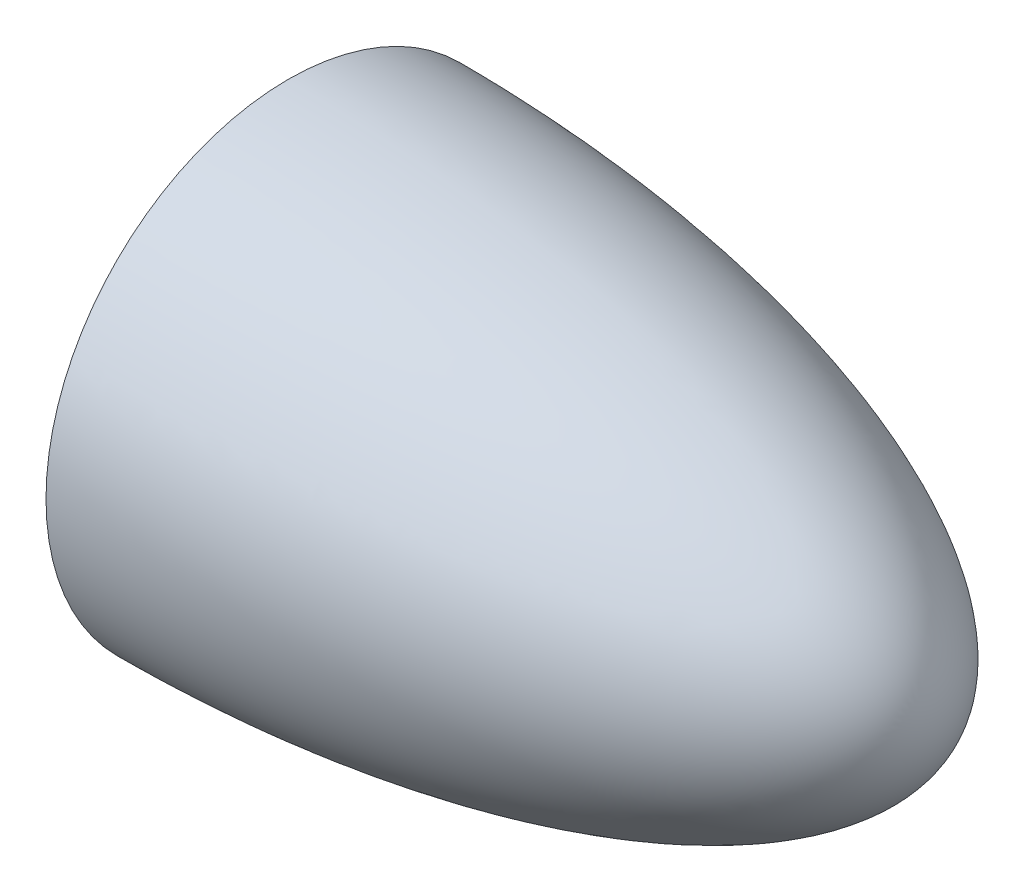
SolidWorks part; units mm, degrees
material "Custom Plastic"
ref_plane "Front Plane" through (0, 0, 0) normal (0, 0, 1) x (1, 0, 0)
ref_plane "Top Plane" through (0, 0, 0) normal (0, 1, 0) x (1, 0, 0)
ref_plane "Right Plane" through (0, 0, 0) normal (1, 0, 0) x (0, 0, -1)
sketch "Sketch1" plane through (0, 0, 0) normal (0, 0, 1) x (1, 0, 0)
  line L4 (0, 38.1) -> (0, 31.75)
  line L5 (95.25, 0) -> (101.6, 0)
  spline S0 degree 4 poles (-10.1599, 37.909) (-9.8428, 37.921) (-9.2082, 37.9439) (-7.937, 37.9857) (-6.3533, 38.028) (-4.7601, 38.0603) (-3.1781, 38.0826) (-1.9201, 38.0945) (-0.3504, 38.1013) (0.9584, 38.0999) (3.0623, 38.087) (4.8396, 38.0587) (7.3853, 38.0054) (10.2567, 37.9131) (13.2403, 37.7849) (16.1477, 37.6205) (18.6059, 37.4591) (20.5529, 37.3152) (22.9983, 37.1167) (25.9229, 36.8484) (29.3352, 36.4907) (33.225, 36.0189) (37.1079, 35.4822) (40.9801, 34.8783) (44.8413, 34.2043) (48.6886, 33.4569) (53.4783, 32.4264) (59.1889, 31.0263) (64.8414, 29.4022) (70.4117, 27.5165) (75.6688, 25.4757) (79.9302, 23.589) (84.0819, 21.4677) (88.0736, 19.0607) (91.0619, 16.9696) (93.6297, 14.8636) (95.7115, 12.8459) (97.2987, 11.0336) (98.5662, 9.3062) (99.542, 7.6977) (100.3319, 6.089) (100.9382, 4.4726) (101.3808, 2.7572) (101.5592, 1.389) (101.6, 0.4832) (101.6, 0) knots 0 0 0 0 0 0.010112 0.020223 0.040447 0.050558 0.06067 0.070782 0.080893 0.096491 0.11209 0.127688 0.143286 0.174482 0.205679 0.221277 0.236875 0.252473 0.268071 0.299268 0.330464 0.36166 0.392857 0.424053 0.45525 0.486446 0.517642 0.580035 0.642428 0.673624 0.70482 0.759552 0.790748 0.821944 0.853141 0.875573 0.896371 0.914156 0.929752 0.94371 0.956194 0.971147 0.984621 1 1 1 1 1 construction
  spline S1 degree 4 poles (0, 38.1) (0.4503, 38.1) (1.3323, 38.0976) (3.0623, 38.087) (4.8396, 38.0587) (7.3853, 38.0054) (10.2567, 37.9131) (13.2403, 37.7849) (16.1477, 37.6205) (18.6059, 37.4591) (20.5529, 37.3152) (22.9983, 37.1167) (25.9229, 36.8484) (29.3352, 36.4907) (33.225, 36.0189) (37.1079, 35.4822) (40.9801, 34.8783) (44.8413, 34.2043) (48.6886, 33.4569) (53.4783, 32.4264) (59.1889, 31.0263) (64.8414, 29.4022) (70.4117, 27.5165) (75.6688, 25.4757) (79.9302, 23.589) (84.0819, 21.4677) (88.0736, 19.0607) (91.0619, 16.9696) (93.6297, 14.8636) (95.7115, 12.8459) (97.2987, 11.0336) (98.5662, 9.3062) (99.542, 7.6977) (100.3319, 6.089) (100.9382, 4.4726) (101.3808, 2.7572) (101.5592, 1.389) (101.6, 0.4832) (101.6, 0) knots 0.080893 0.080893 0.080893 0.080893 0.080893 0.096491 0.11209 0.127688 0.143286 0.174482 0.205679 0.221277 0.236875 0.252473 0.268071 0.299268 0.330464 0.36166 0.392857 0.424053 0.45525 0.486446 0.517642 0.580035 0.642428 0.673624 0.70482 0.759552 0.790748 0.821944 0.853141 0.875573 0.896371 0.914156 0.929752 0.94371 0.956194 0.971147 0.984621 1 1 1 1 1
  spline S2 degree 4 poles (-9.5317, 31.5909) (-9.2209, 31.6008) (-8.612, 31.6199) (-7.5089, 31.6548) (-5.5371, 31.697) (-3.7696, 31.7318) (-1.0753, 31.7505) (0.5734, 31.7519) (2.5547, 31.7409) (3.8258, 31.7252) (4.9811, 31.7072) (5.8817, 31.69) (7.0125, 31.6649) (8.3698, 31.629) (9.9525, 31.5786) (11.7612, 31.5095) (13.5692, 31.4286) (15.3768, 31.336) (17.1837, 31.2316) (18.9899, 31.1151) (21.2466, 30.9545) (24.8549, 30.665) (28.9087, 30.2742) (33.4038, 29.7537) (37.8873, 29.1423) (42.3604, 28.4597) (47.7091, 27.5214) (53.0277, 26.4219) (58.3048, 25.1389) (63.5381, 23.6899) (68.7187, 22.0588) (73.8319, 20.1564) (78.8058, 17.9127) (82.8075, 15.7488) (85.6346, 13.9649) (88.0438, 12.1762) (89.9543, 10.4913) (91.3784, 9.0129) (92.5158, 7.6035) (93.3718, 6.3271) (94.0371, 5.1082) (94.5319, 3.9583) (94.8869, 2.8578) (95.1331, 1.7294) (95.2276, 0.8838) (95.25, 0.3091) (95.25, 0) knots 0 0 0 0 0 0.0103 0.020601 0.041202 0.061803 0.082404 0.098059 0.113714 0.121542 0.12937 0.137197 0.145025 0.16068 0.176335 0.19199 0.207646 0.223301 0.238956 0.254611 0.270266 0.301577 0.364198 0.395508 0.426818 0.458129 0.52075 0.58337 0.614681 0.645991 0.708612 0.771233 0.803294 0.834605 0.865915 0.886788 0.906995 0.922648 0.93685 0.949372 0.960098 0.970627 0.980098 0.989316 1 1 1 1 1 construction
  spline S3 degree 4 poles (0, 31.75) (0.4152, 31.75) (1.2567, 31.7481) (2.5547, 31.7409) (3.8258, 31.7252) (4.9811, 31.7072) (5.8817, 31.69) (7.0125, 31.6649) (8.3698, 31.629) (9.9525, 31.5786) (11.7612, 31.5095) (13.5692, 31.4286) (15.3768, 31.336) (17.1837, 31.2316) (18.9899, 31.1151) (21.2466, 30.9545) (24.8549, 30.665) (28.9087, 30.2742) (33.4038, 29.7537) (37.8873, 29.1423) (42.3604, 28.4597) (47.7091, 27.5214) (53.0277, 26.4219) (58.3048, 25.1389) (63.5381, 23.6899) (68.7187, 22.0588) (73.8319, 20.1564) (78.8058, 17.9127) (82.8075, 15.7488) (85.6346, 13.9649) (88.0438, 12.1762) (89.9543, 10.4913) (91.3784, 9.0129) (92.5158, 7.6035) (93.3718, 6.3271) (94.0371, 5.1082) (94.5319, 3.9583) (94.8869, 2.8578) (95.1331, 1.7294) (95.2276, 0.8838) (95.25, 0.3091) (95.25, 0) knots 0.082404 0.082404 0.082404 0.082404 0.082404 0.098059 0.113714 0.121542 0.12937 0.137197 0.145025 0.16068 0.176335 0.19199 0.207646 0.223301 0.238956 0.254611 0.270266 0.301577 0.364198 0.395508 0.426818 0.458129 0.52075 0.58337 0.614681 0.645991 0.708612 0.771233 0.803294 0.834605 0.865915 0.886788 0.906995 0.922648 0.93685 0.949372 0.960098 0.970627 0.980098 0.989316 1 1 1 1 1
revolve "Revolve2" add sketch "Sketch1" angle 360 about L5
